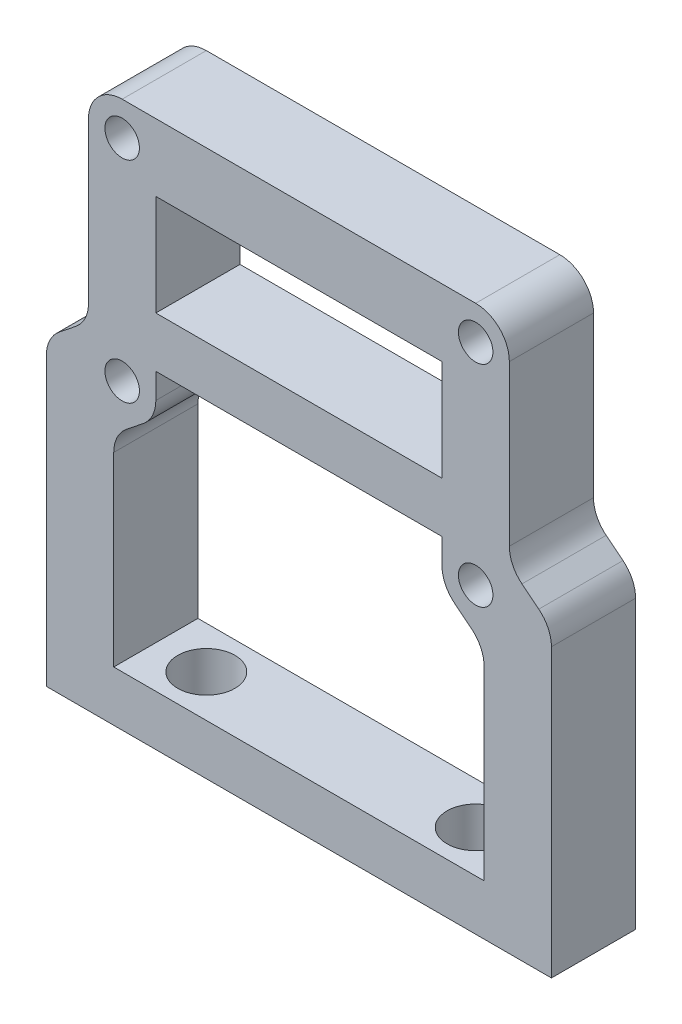
SolidWorks part; units mm, degrees
ref_plane "Front Plane" through (0, 0, 0) normal (0, 0, 1) x (1, 0, 0)
ref_plane "Top Plane" through (0, 0, 0) normal (0, 1, 0) x (1, 0, 0)
ref_plane "Right Plane" through (0, 0, 0) normal (1, 0, 0) x (0, 0, -1)
sketch "Sketch1" plane through (0, 0, 0) normal (0, 0, 1) x (1, 0, 0)
  line L0 (0, 0) -> (0, 119.7462) construction
  line L1 (-15, 0) -> (15, 0)
  line L2 (-15, 0) -> (-15, 18)
  line L3 (-15, 18) -> (-12.5, 20)
  line L4 (15, 0) -> (15, 18)
  line L5 (-12.5, 32.4612) -> (12.5, 32.4612)
  line L6 (-12.5, 32.4612) -> (-12.5, 20)
  line L7 (12.5, 20) -> (15, 18)
  line L8 (12.5, 32.4612) -> (12.5, 20)
  line L9 (-11, 15) -> (-8.5, 17)
  line L10 (-8.5, 19.4612) -> (8.5, 19.4612)
  line L11 (-11, 15) -> (-11, 3)
  line L12 (-11, 3) -> (11, 3)
  line L13 (11, 15) -> (11, 3)
  line L14 (-8.5, 28.4612) -> (8.5, 28.4612)
  line L15 (-8.5, 28.4612) -> (-8.5, 22.4612)
  line L16 (11, 15) -> (8.5, 17)
  line L17 (8.5, 28.4612) -> (8.5, 22.4612)
  line L18 (-8.5, 22.4612) -> (8.5, 22.4612)
  line L19 (-8.5, 19.4612) -> (-8.5, 17)
  line L20 (8.5, 19.4612) -> (8.5, 17)
  circle A0 centre (-10.5, 30.4612) radius 0.25
  circle A1 centre (-10.5, 17.9612) radius 0.25
  circle A2 centre (10.5, 30.4612) radius 0.25
  circle A3 centre (10.5, 17.9612) radius 0.25
  point P12 (0, 0)
  point P17 (0, 3)
  point P22 (0, 28.4612)
  point P23 (0, 32.4612)
  dimension "D8" = 0.5
  dimension "D9" = 0.5
  dimension "D10" = 10.5
  dimension "D2" = 3
  dimension "D3" = 22
  dimension "D4" = 30
  dimension "D5" = 12
  dimension "D6" = 25
  dimension "D7" = 18
  dimension "D11" = 2
  dimension "D12" = 12.5
  dimension "D13" = 2
  dimension "D14" = 4
  dimension "D15" = 4
  dimension "D16" = 17
  dimension "D17" = 3
  dimension "D18" = 8
extrude "Boss-Extrude1" add sketch "Sketch1" along normal blind 5
fillet "Fillet1" radius 2 10 edges at (12.5, 20, 2.5) (15, 18, 2.5) (11, 15, 2.5) (8.5, 17, 2.5) (-11, 15, 2.5) (-8.5, 17, 2.5) (12.5, 32.4612, 2.5) (-12.5, 32.4612, 2.5) (-12.5, 20, 2.5) (-15, 18, 2.5)
hole_wizard "M2.5x0.45 Tapped Hole1" positions "Sketch2" profile "Sketch3" tap size "M2.5x0.45" standard "ANSI Metric" end condition through all
sketch "Sketch2" plane through (0, 0, 5) normal (0, 0, 1) x (1, 0, 0)
  point P4 (-10.5, 17.9612)
  point P7 (10.5, 30.4612)
  point P10 (10.5, 17.9612)
  point P20 (-10.5, 30.4612)
sketch "Sketch3" plane through (-10.5, 17.9612, 5) normal (1, 0, 0) x (0, -1, 0)
  line L0 (0, 0) -> (0, 5)
  line L1 (0, 5) -> (1.025, 5)
  line L2 (1.025, 5) -> (1.025, 0)
  line L5 (1.025, 0) -> (0, 0)
  line L11 (0, -6.35) -> (0, 107.95) construction
  dimension "Thru Tap Drill Dia." = 2.05
  dimension "Thru Tap Drill Depth" = 5
cosmetic thread "Hole Thread1" parameters "D2"=2.5
cosmetic thread "Hole Thread2" parameters "D2"=2.5
cosmetic thread "Hole Thread3" parameters "D2"=2.5
cosmetic thread "Hole Thread4" parameters "D2"=2.5
hole_wizard "M3 Clearance Hole1" positions "Sketch4" profile "Sketch5" hole size "M3" standard "ANSI Metric" end condition up to next
sketch "Sketch4" plane through (0, 0, 0) normal (0, -1, 0) x (-1, 0, 0)
  line L0 (0, 0) -> (0, -5) construction
  line L1 (15, 0) -> (-15, 0) construction
  line L2 (15, -5) -> (-15, -5) construction
  line L4 (15, -2.5) -> (-15, -2.5) construction
  line L5 (15, -5) -> (15, 0) construction
  line L6 (-15, -5) -> (-15, 0) construction
  point P0 (8, -2.5)
  point P2 (-8, -2.5)
  dimension "D1" = 16
  dimension "D2" = 8
sketch "Sketch5" plane through (-8, 0, 2.5) normal (1, 0, 0) x (0, 0, -1)
  line L0 (0, 0) -> (0, 3)
  line L1 (0, 3) -> (1.7, 3)
  line L2 (1.7, 3) -> (1.7, 0)
  line L5 (1.7, 0) -> (0, 0)
  line L11 (0, -6.35) -> (0, 107.95) construction
  dimension "Thru Hole Dia." = 3.4
  dimension "Thru Hole Depth" = 3
